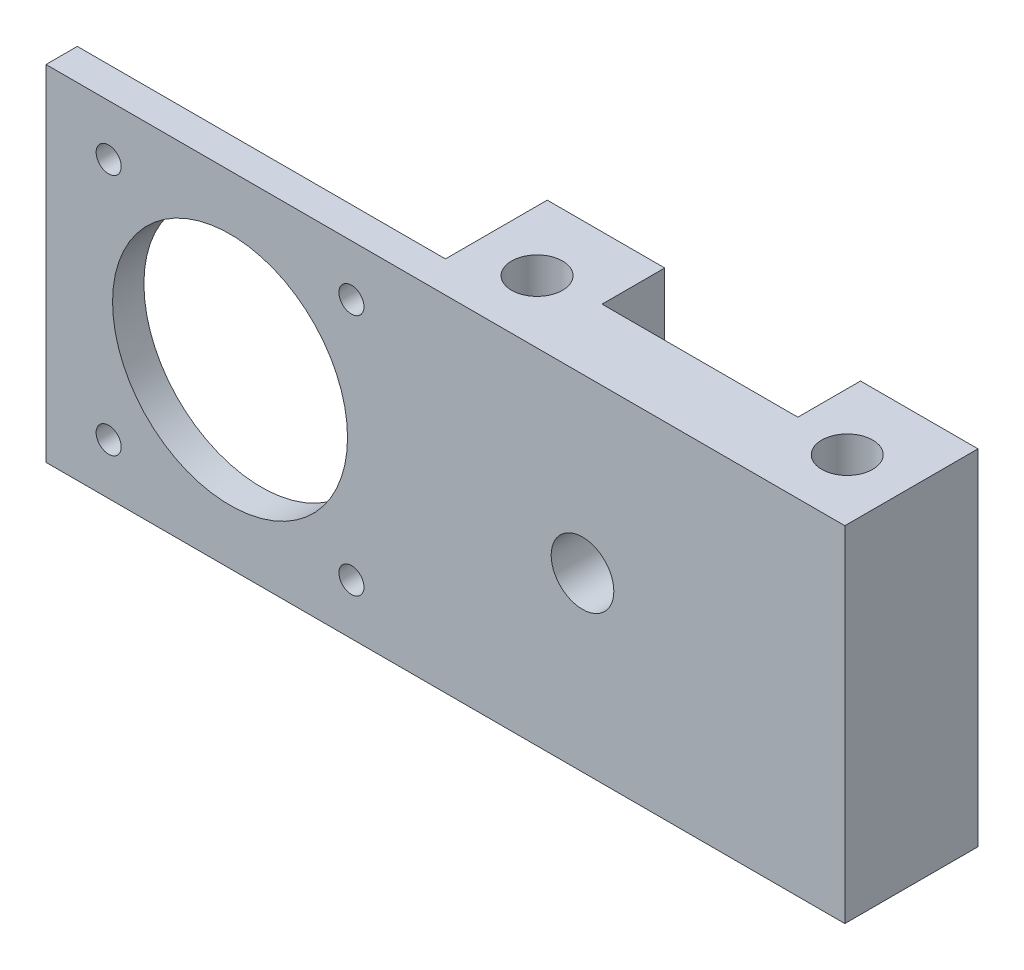
SolidWorks part; units mm, degrees
ref_plane "Спереди" through (0, 0, 0) normal (0, 0, 1) x (1, 0, 0)
ref_plane "Сверху" through (0, 0, 0) normal (0, 1, 0) x (1, 0, 0)
ref_plane "Справа" through (0, 0, 0) normal (1, 0, 0) x (0, 0, -1)
sketch "Эскиз1" plane through (0, 0, 0) normal (0, 0, 1) x (1, 0, 0)
  line L1 (-27.5, -22) -> (27.5, -22)
  line L2 (-27.5, -22) -> (-27.5, 22)
  line L3 (-27.5, 22) -> (27.5, 22)
  line L4 (27.5, -22) -> (27.5, 22)
  line L5 (-27.5, -22) -> (27.5, 22) construction
  line L6 (-27.5, 22) -> (27.5, -22) construction
  point P0 (0, 0)
  dimension "D1" = 55
  dimension "D2" = 44
extrude "Бобышка-Вытянуть1" add sketch "Эскиз1" along normal blind 18
sketch "Эскиз2" plane through (0, 0, 18) normal (0, 0, 1) x (1, 0, 0)
  circle A0 centre (-6, 0) radius 4
  dimension "D1" = 8
  dimension "D2" = 6
extrude "Вырез-Вытянуть1" cut sketch "Эскиз2" against normal blind 18
hole_wizard "Диаметр отверстия Ø6.5 (6.5)1" positions "Эскиз3" profile "Эскиз4" hole size "Ø6.5" standard "DIN" end condition through all
sketch "Эскиз3" plane through (0, 22, 0) normal (0, 1, 0) x (1, 0, 0)
  line L0 (27.5, 0) -> (-27.5, 0) construction
  point P0 (19.8, -9)
  point P2 (-19.8, -9)
  dimension "D1" = 9
  dimension "D2" = 19.8
  dimension "D3" = 39.6
sketch "Эскиз4" plane through (19.8, 22, 9) normal (1, 0, 0) x (0, 0, 1)
  line L0 (0, 0) -> (0, 44)
  line L1 (0, 44) -> (3.25, 44)
  line L2 (3.25, 44) -> (3.25, 0)
  line L5 (3.25, 0) -> (0, 0)
  line L11 (0, -6.35) -> (0, 107.95) construction
  dimension "Диаметр сквозного отверстия" = 6.5
  dimension "Глубина сквозного отверстия" = 44
sketch "Эскиз5" plane through (0, 0, 0) normal (0, 0, -1) x (-1, 0, 0)
  line L1 (12.5, 25) -> (-12.5, 25)
  line L2 (12.5, 25) -> (12.5, -25)
  line L3 (12.5, -25) -> (-12.5, -25)
  line L4 (-12.5, 25) -> (-12.5, -25)
  line L5 (12.5, 25) -> (-12.5, -25) construction
  line L6 (12.5, -25) -> (-12.5, 25) construction
  point P0 (0, 0)
  dimension "D1" = 25
  dimension "D2" = 50
extrude "Вырез-Вытянуть2" cut sketch "Эскиз5" against normal blind 8
sketch "Эскиз6" plane through (0, 0, 18) normal (0, 0, 1) x (1, 0, 0)
  line L0 (-27.5, 22) -> (-27.5, -22) construction
  line L1 (-74.5, -22) -> (-27.5, -22)
  line L2 (-74.5, -22) -> (-74.5, 22)
  line L3 (-74.5, 22) -> (-27.5, 22)
  line L4 (-27.5, -22) -> (-27.5, 22)
  line L5 (-74.5, -22) -> (-27.5, 22) construction
  line L6 (-74.5, 22) -> (-27.5, -22) construction
  circle A0 centre (-6, 0) radius 4 construction
  circle A1 centre (-51, 0) radius 15
  point P0 (-51, 0)
  dimension "D1" = 45
  dimension "D3" = 30
  dimension "D2" = 44
extrude "Бобышка-Вытянуть2" add sketch "Эскиз6" against normal blind 5
hole_wizard "Диаметр отверстия Ø3.2 (3.2)1" positions "Эскиз7" profile "Эскиз8" hole size "Ø3.2" standard "DIN" end condition through all
sketch "Эскиз7" plane through (0, 0, 13) normal (0, 0, -1) x (-1, 0, 0)
  circle A0 centre (51, 0) radius 15 construction
  point P0 (35.5, -15.5)
  dimension "D1" = 15.5
  dimension "D2" = 15.5
sketch "Эскиз8" plane through (-35.5, -15.5, 13) normal (1, 0, 0) x (0, 1, 0)
  line L0 (0, 0) -> (0, 5)
  line L1 (0, 5) -> (1.6, 5)
  line L2 (1.6, 5) -> (1.6, 0)
  line L5 (1.6, 0) -> (0, 0)
  line L11 (0, -6.35) -> (0, 107.95) construction
  dimension "Диаметр сквозного отверстия" = 3.2
  dimension "Глубина сквозного отверстия" = 5
pattern_circular "Круговой массив1" count 4 over 360 about axis through (-51, 0, 0) along (0, 0, 1) of "Диаметр отверстия Ø3.2 (3.2)1"
sketch "Эскиз9" plane through (0, 0, 18) normal (0, 0, 1) x (1, 0, 0)
  line L1 (-100, -50) -> (100, -50)
  line L2 (-100, -50) -> (-100, 50)
  line L3 (-100, 50) -> (100, 50)
  line L4 (100, -50) -> (100, 50)
  line L5 (-100, -50) -> (100, 50) construction
  line L6 (-100, 50) -> (100, -50) construction
  point P0 (0, 0)
  dimension "D1" = 200
  dimension "D2" = 100
extrude "Вырез-Вытянуть3" cut sketch "Эскиз9" against normal blind 1
